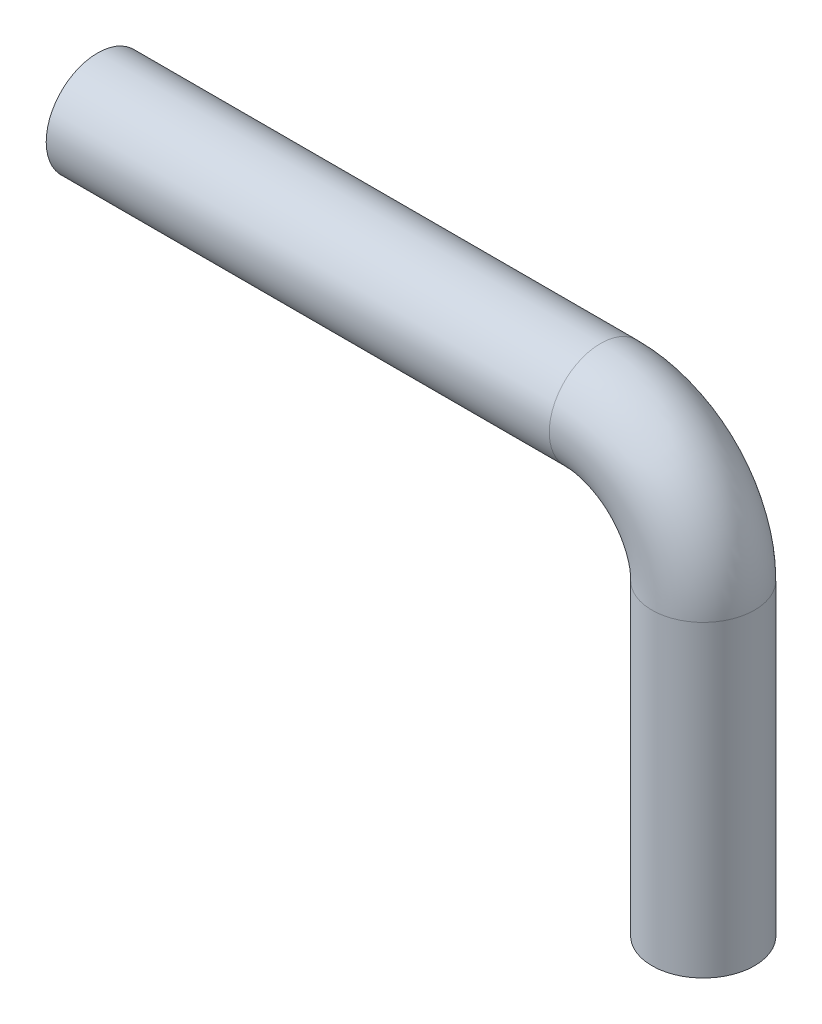
SolidWorks part; units mm, degrees
ref_plane "Piano frontale" through (0, 0, 0) normal (0, 0, 1) x (1, 0, 0)
ref_plane "Piano superiore" through (0, 0, 0) normal (0, 1, 0) x (1, 0, 0)
ref_plane "Piano destro" through (0, 0, 0) normal (1, 0, 0) x (0, 0, -1)
sketch "Schizzo1" plane through (0, 0, 0) normal (0, 0, 1) x (1, 0, 0)
  line L0 (0, 0) -> (49, 0)
  line L1 (59, -10) -> (59, -40)
  arc A0 (49, 0) -> (59, -10) centre (49, -10) cw
  dimension "D1" = 10
  dimension "D2" = 49
  dimension "D3" = 30
sweep "Sweep1" add path "Schizzo1" circular profile diameter 10 parameters "D3"=10
